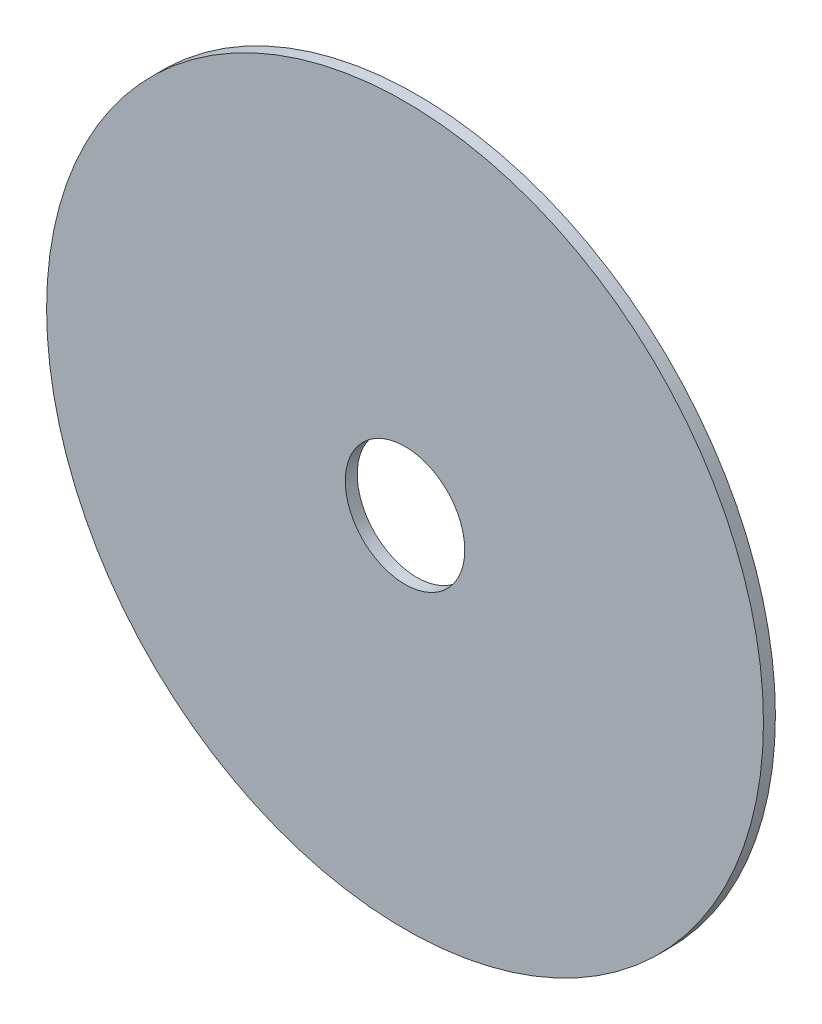
SolidWorks part; units mm, degrees
ref_plane "Front Plane" through (0, 0, 0) normal (0, 0, 1) x (1, 0, 0)
ref_plane "Top Plane" through (0, 0, 0) normal (0, 1, 0) x (1, 0, 0)
ref_plane "Right Plane" through (0, 0, 0) normal (1, 0, 0) x (0, 0, -1)
sketch "Sketch1" plane through (0, 0, 0) normal (0, 0, 1) x (1, 0, 0)
  circle A0 centre (0, 0) radius 30
extrude "Boss-Extrude1" add sketch "Sketch1" along normal blind 1
sketch "Sketch2" plane through (0, 0, 1) normal (0, 0, 1) x (1, 0, 0)
  circle A0 centre (0, 0) radius 5
extrude "Cut-Extrude1" cut sketch "Sketch2" against normal blind 4
